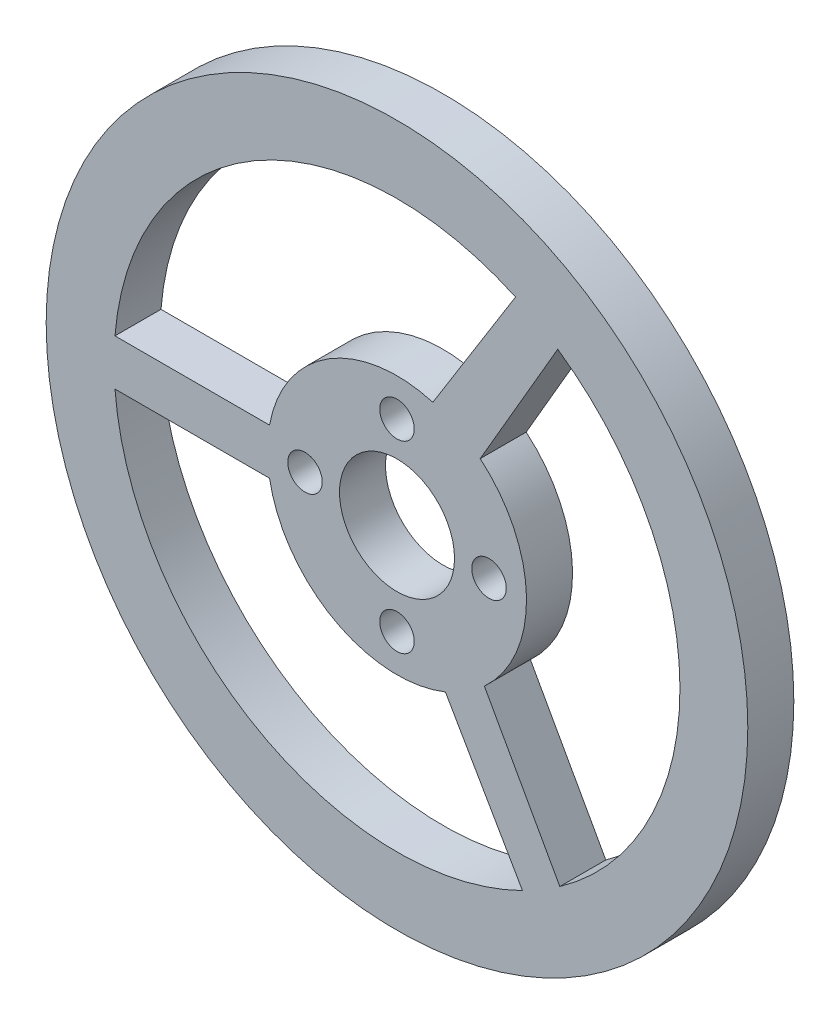
SolidWorks part; units mm, degrees
ref_plane "前视基准面" through (0, 0, 0) normal (0, 0, 1) x (1, 0, 0)
ref_plane "上视基准面" through (0, 0, 0) normal (0, 1, 0) x (1, 0, 0)
ref_plane "右视基准面" through (0, 0, 0) normal (1, 0, 0) x (0, 0, -1)
sketch "草图1" plane through (0, 0, 0) normal (0, 0, 1) x (1, 0, 0)
  circle A0 centre (0, 0) radius 30.5
  dimension "D1" = 61
extrude "凸台-拉伸1" add sketch "草图1" along normal blind 4
sketch "草图2" plane through (0, 0, 4) normal (0, 0, 1) x (1, 0, 0)
  line L1 (15.8601, -27.4705) -> (5.6306, -9.7526) construction
  line L2 (-24.5192, -2) -> (-11.0823, -2)
  line L3 (-24.5192, 2) -> (-11.0823, 2)
  line L4 (14.1555, -20.12) -> (7.5971, -8.3127)
  line L5 (10.9094, -22.0495) -> (4.2095, -10.4449)
  line L6 (13.976, 20.2451) -> (7.2322, 8.632)
  line L7 (10.3049, 22.3384) -> (3.1175, 10.8212)
  circle A0 centre (0, 0) radius 5
  circle A2 centre (-8, 0) radius 1.5
  circle A3 centre (0, 8) radius 1.5
  circle A4 centre (8, 0) radius 1.5
  circle A5 centre (0, -8) radius 1.5
  arc A6 (-24.5192, -2) -> (10.9094, -22.0495) centre (0, 0) ccw
  arc A10 (-11.0823, -2) -> (4.2095, -10.4449) centre (0, 0) ccw
  arc A11 (7.5971, -8.3127) -> (7.2322, 8.632) centre (0, 0) ccw
  arc A12 (14.1555, -20.12) -> (13.976, 20.2451) centre (0, 0) ccw
  arc A13 (3.1175, 10.8212) -> (-11.0823, 2) centre (0, 0) ccw
  arc A14 (10.3049, 22.3384) -> (-24.5192, 2) centre (0, 0) ccw
  point P14 (0, 0)
  point P21 (0, 0)
  dimension "D1" = 10
  dimension "D3" = 3
  dimension "D4" = 4
extrude "切除-拉伸1" cut sketch "草图2" against normal up to next
